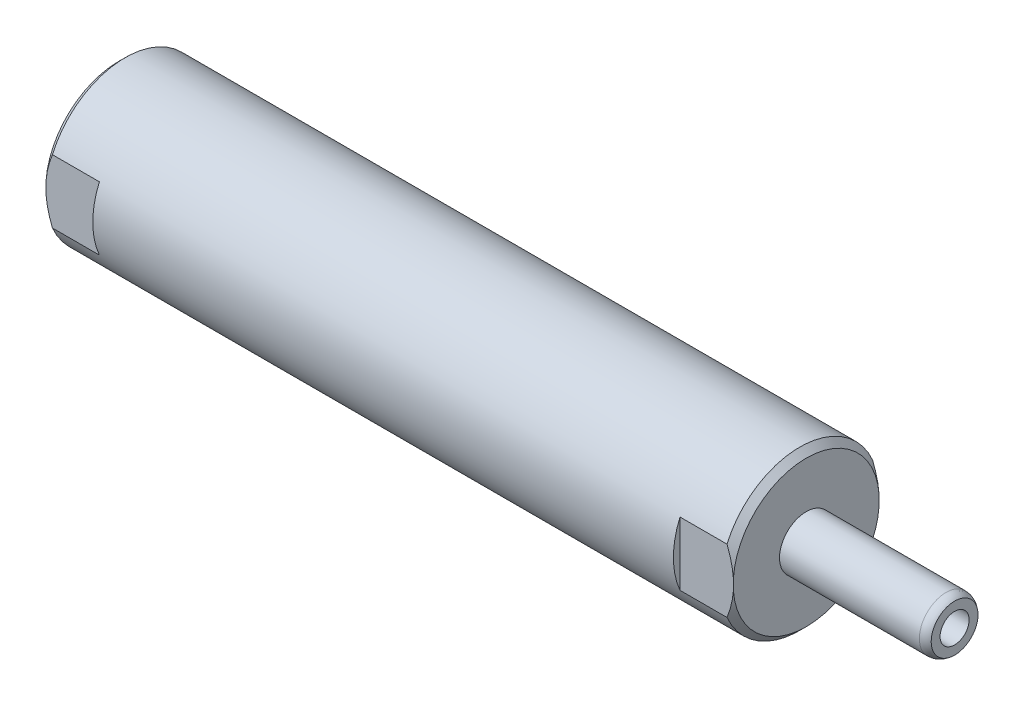
SolidWorks part; units mm, degrees
material "Alloy Steel"
ref_plane "Front Plane" through (0, 0, 0) normal (0, 0, 1) x (1, 0, 0)
ref_plane "Top Plane" through (0, 0, 0) normal (0, 1, 0) x (1, 0, 0)
ref_plane "Right Plane" through (0, 0, 0) normal (1, 0, 0) x (0, 0, -1)
ref_plane "Plane1" through (0, 0, 0) normal (0, 0, -1) x (-1, 0, 0)
sketch "Sketch1" plane through (0, 0, 0) normal (0, 0, -1) x (-1, 0, 0)
  line L0 (-99.4156, 2.7869) -> (-99.4156, 0)
  line L1 (-99.4156, 0) -> (0, 0)
  line L2 (0, 0) -> (0, 9.4488)
  line L4 (0, 9.4488) -> (-81.7626, 9.4488)
  line L6 (-81.7626, 9.4488) -> (-81.7626, 3.175)
  line L7 (-81.7626, 3.175) -> (-98.3996, 3.175)
  line L8 (-99.4156, 0) -> (0, 0) construction
  line L9 (0, 0) -> (6.3339, 0) construction
  arc A0 (-98.3996, 3.175) -> (-99.4156, 2.7869) centre (-98.3996, 1.651) ccw
  dimension "D6" = 1.524
  dimension "D1" = 18.8976
  dimension "D4" = 6.35
  dimension "D5" = 1.016
  dimension "D7" = 17.653
  dimension "D8" = 81.7626
revolve "Revolve1" add sketch "Sketch1" angle 360 about L8
sketch "Sketch2" plane through (0, 0, 0) normal (0, 0, -1) x (-1, 0, 0)
  line L0 (-13.97, 4.9784) -> (-13.97, 0)
  line L1 (-13.97, 0) -> (0, 0)
  line L2 (0, 0) -> (0, 6.1849)
  line L3 (0, 6.1849) -> (-2.5527, 5.6423)
  line L4 (-2.5527, 5.6423) -> (-3.2166, 4.9784)
  line L5 (-3.2166, 4.9784) -> (-13.97, 4.9784)
  line L6 (-13.97, 0) -> (0, 0) construction
revolve "Cut-Revolve1" cut sketch "Sketch2" angle 360 about L6
sketch "Sketch3" plane through (0, 0, 0) normal (0, 0, -1) x (-1, 0, 0)
  line L0 (-99.4156, 1.7272) -> (-99.4156, 0)
  line L1 (-99.4156, 0) -> (-93.0656, 0)
  line L2 (-93.0656, 0) -> (-94.1034, 1.7272)
  line L3 (-94.1034, 1.7272) -> (-99.4156, 1.7272)
  line L4 (-66.3139, 0) -> (-46.9899, 0) construction
  line L5 (-99.4156, 2.7869) -> (-99.4156, -2.7869) construction
  dimension "D1" = 3.4544
  dimension "D2" = 6.35
  dimension "D3" = 59
revolve "Cut-Revolve2" cut sketch "Sketch3" angle 360 about L4
chamfer "Chamfer1" distance 0.762 angle 45 2 edges at (0, 0, 9.4488) (81.7626, 0, 9.4488)
sketch "Sketch5" plane through (0, 0, 0) normal (0, 1, 0) x (1, 0, 0)
  line L0 (0, 0) -> (18.2862, 0) construction
  line L1 (0, 8.6614) -> (6.35, 8.6614)
  line L2 (6.35, 8.6614) -> (6.35, 9.4488)
  line L3 (81.0006, 9.4488) -> (0.762, 9.4488) construction
  line L4 (6.35, 9.4488) -> (0, 9.4488)
  line L5 (0, 9.4488) -> (0, 8.6614)
  line L6 (0, 8.6868) -> (0, -8.6868) construction
  line L7 (0, -9.4488) -> (0, -8.6614)
  line L8 (6.35, -9.4488) -> (0, -9.4488)
  line L9 (6.35, -8.6614) -> (6.35, -9.4488)
  line L10 (0, -8.6614) -> (6.35, -8.6614)
  dimension "D1" = 90
  dimension "D2" = 6.35
  dimension "D3" = 17.3228
extrude "Cut-Extrude1" cut sketch "Sketch5" against normal through all and the other way through all
sketch "Sketch6" plane through (0, 0, 0) normal (0, 1, 0) x (1, 0, 0)
  line L0 (81.7626, -8.6868) -> (81.7626, 8.6868) construction
  line L1 (81.7626, 8.6614) -> (75.4126, 8.6614)
  line L2 (81.7626, 8.6614) -> (81.7626, 9.4488)
  line L3 (81.7626, 9.4488) -> (75.4126, 9.4488)
  line L4 (75.4126, 8.6614) -> (75.4126, 9.4488)
  line L5 (81.0006, 9.4488) -> (6.35, 9.4488) construction
  line L6 (6.35, -9.4488) -> (81.0006, -9.4488) construction
  line L7 (81.7626, -8.6614) -> (75.4126, -8.6614)
  line L8 (81.7626, -8.6614) -> (81.7626, -9.4488)
  line L9 (81.7626, -9.4488) -> (75.4126, -9.4488)
  line L10 (75.4126, -8.6614) -> (75.4126, -9.4488)
  dimension "D1" = 6.35
  dimension "D2" = 17.3228
extrude "Cut-Extrude2" cut sketch "Sketch6" against normal through all and the other way through all
